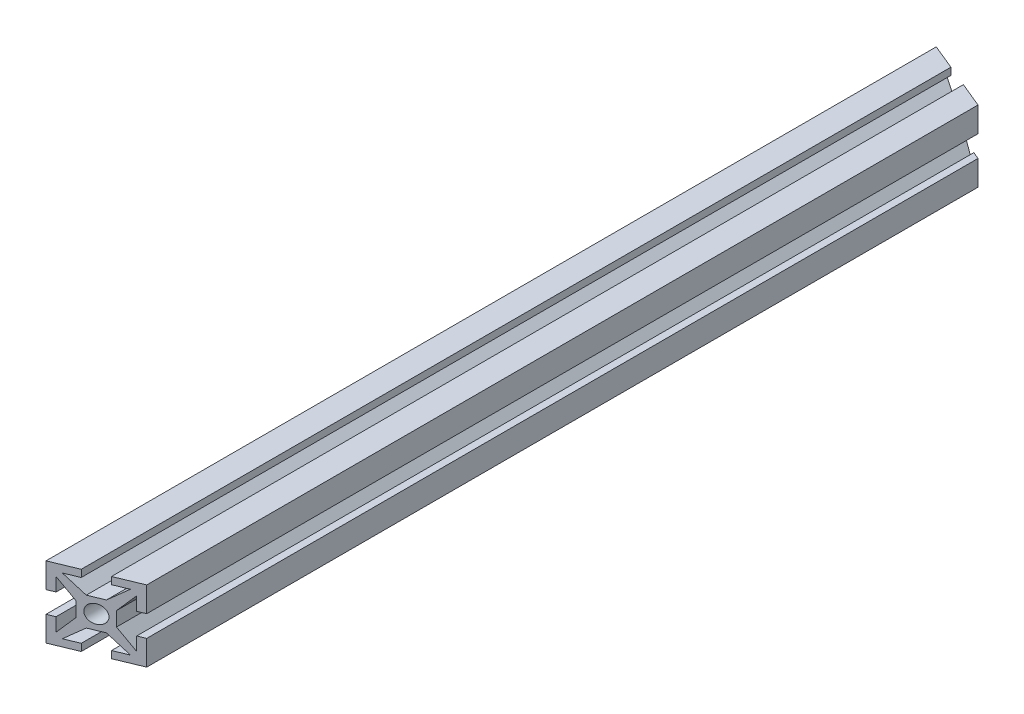
SolidWorks part; units mm, degrees
ref_plane "Front Plane" through (0, 0, 0) normal (0, 0, 1) x (1, 0, 0)
ref_plane "Top Plane" through (0, 0, 0) normal (0, 1, 0) x (1, 0, 0)
ref_plane "Right Plane" through (0, 0, 0) normal (1, 0, 0) x (0, 0, -1)
sketch "Esquisse2" plane through (0, 0, 0) normal (0, 0, 1) x (1, 0, 0)
  line L0 (-1, -2) -> (1, -2)
  line L1 (1, -2) -> (3.3835, -4)
  line L2 (3.3835, -4) -> (1.5, -4)
  line L3 (1.5, -4) -> (1.5, -5)
  line L4 (1.5, -5) -> (5, -5)
  line L5 (-1, -2) -> (-3.3835, -4)
  line L6 (-3.3835, -4) -> (-1.5, -4)
  line L7 (-1.5, -4) -> (-1.5, -5)
  line L8 (-1.5, -5) -> (-5, -5)
  line L9 (-5, -5) -> (-5, -1.5)
  line L10 (-5, -1.5) -> (-4, -1.5)
  line L11 (-4, -1.5) -> (-4, -3.3835)
  line L12 (-4, -3.3835) -> (-2, -1)
  line L13 (-2, -1) -> (-2, 1)
  line L14 (-2, 1) -> (-4, 3.3835)
  line L15 (-4, 3.3835) -> (-4, 1.5)
  line L16 (-4, 1.5) -> (-5, 1.5)
  line L17 (-5, 1.5) -> (-5, 5)
  line L18 (-5, 5) -> (-1.5, 5)
  line L19 (-1.5, 5) -> (-1.5, 4)
  line L20 (-1.5, 4) -> (-3.3835, 4)
  line L21 (-3.3835, 4) -> (-1, 2)
  line L22 (-1, 2) -> (1, 2)
  line L23 (1, 2) -> (3.3835, 4)
  line L24 (3.3835, 4) -> (1.5, 4)
  line L25 (1.5, 4) -> (1.5, 5)
  line L26 (1.5, 5) -> (5, 5)
  line L27 (5, 5) -> (5, 1.5)
  line L28 (5, 1.5) -> (4, 1.5)
  line L29 (4, 1.5) -> (4, 3.3835)
  line L30 (4, 3.3835) -> (2, 1)
  line L31 (2, -1) -> (2, 1)
  line L32 (2, -1) -> (4, -3.3835)
  line L33 (4, -3.3835) -> (4, -1.5)
  line L34 (4, -1.5) -> (5, -1.5)
  line L35 (5, -1.5) -> (5, -5)
  circle A0 centre (0, 0) radius 1.25
  point P4 (0, -2)
  point P34 (0, 2)
  point P40 (2, 0)
  dimension "D4" = 2.5
  dimension "D1" = 2
  dimension "D2" = 3.5
  dimension "D3" = 1
  dimension "D5" = 10
  dimension "D6" = 10
  dimension "D7" = 140
  dimension "D8" = 4
  dimension "D9" = 4
  dimension "D10" = 3.5
  dimension "D11" = 3
extrude "Boss.-Extru.1" add sketch "Esquisse2" along normal blind 125
sketch "Esquisse3" plane through (0, 5, 0) normal (0, 1, 0) x (1, 0, 0)
  line L0 (-5, 0) -> (5, 0)
  line L1 (-1.5, 0) -> (-5, 0) construction
  line L2 (5, 0) -> (5, -4.1421)
  line L3 (5, -125) -> (5, 0) construction
  line L4 (5, -4.1421) -> (-5, 0)
  line L5 (-5, -125) -> (-5, 0) construction
  line L6 (5, -120.8579) -> (-5, -125)
  line L7 (-5, -125) -> (5, -125)
  line L8 (5, -125) -> (5, -120.8579)
  dimension "D1" = 67.5
  dimension "D2" = 22.5
extrude "Enlèv. mat.-Extru.1" cut sketch "Esquisse3" against normal through all
